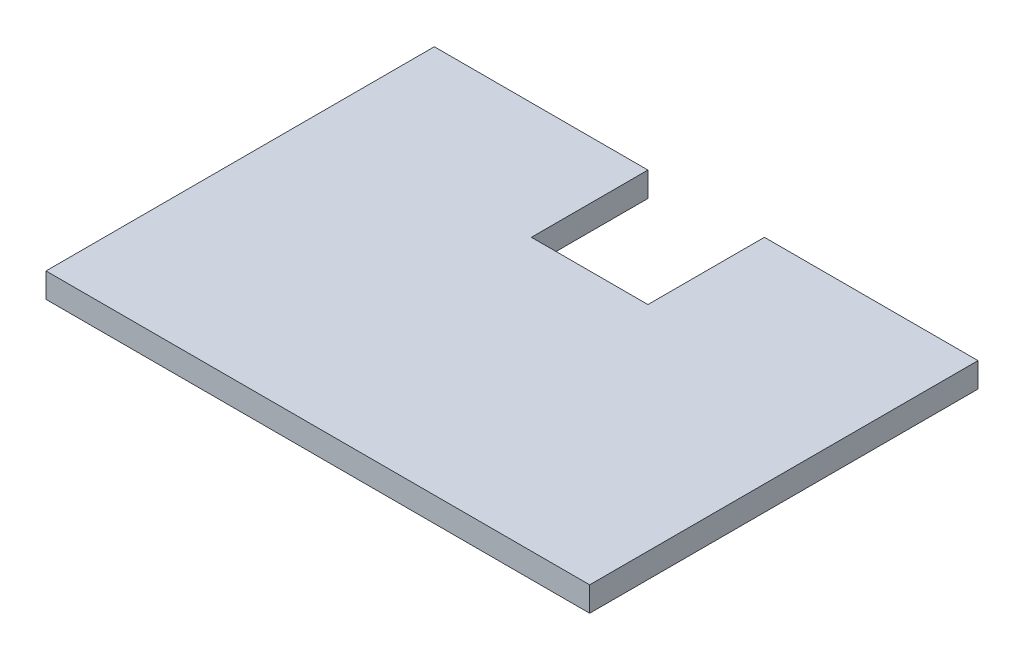
SolidWorks part; units mm, degrees
ref_plane "Front Plane" through (0, 0, 0) normal (0, 0, 1) x (1, 0, 0)
ref_plane "Top Plane" through (0, 0, 0) normal (0, 1, 0) x (1, 0, 0)
ref_plane "Right Plane" through (0, 0, 0) normal (1, 0, 0) x (0, 0, -1)
sketch "Sketch1" plane through (0, 0, 0) normal (0, 1, 0) x (1, 0, 0)
  line L1 (-35, 25) -> (35, 25)
  line L2 (-35, 25) -> (-35, -25)
  line L3 (-35, -25) -> (35, -25)
  line L4 (35, 25) -> (35, -25)
  line L5 (-35, 25) -> (35, -25) construction
  line L6 (-35, -25) -> (35, 25) construction
  point P0 (0, 0)
  dimension "D1" = 70
  dimension "D2" = 50
extrude "Boss-Extrude1" add sketch "Sketch1" along normal blind 3.175
sketch "Sketch2" plane through (0, 3.175, 0) normal (0, 1, 0) x (1, 0, 0)
  line L0 (35, 25) -> (-35, 25) construction
  line L1 (-7.5, 25) -> (7.5, 25)
  line L2 (-7.5, 25) -> (-7.5, 10)
  line L3 (-7.5, 10) -> (7.5, 10)
  line L4 (7.5, 25) -> (7.5, 10)
  point P6 (0, 10)
  dimension "D1" = 15
extrude "Cut-Extrude1" cut sketch "Sketch2" against normal through all
